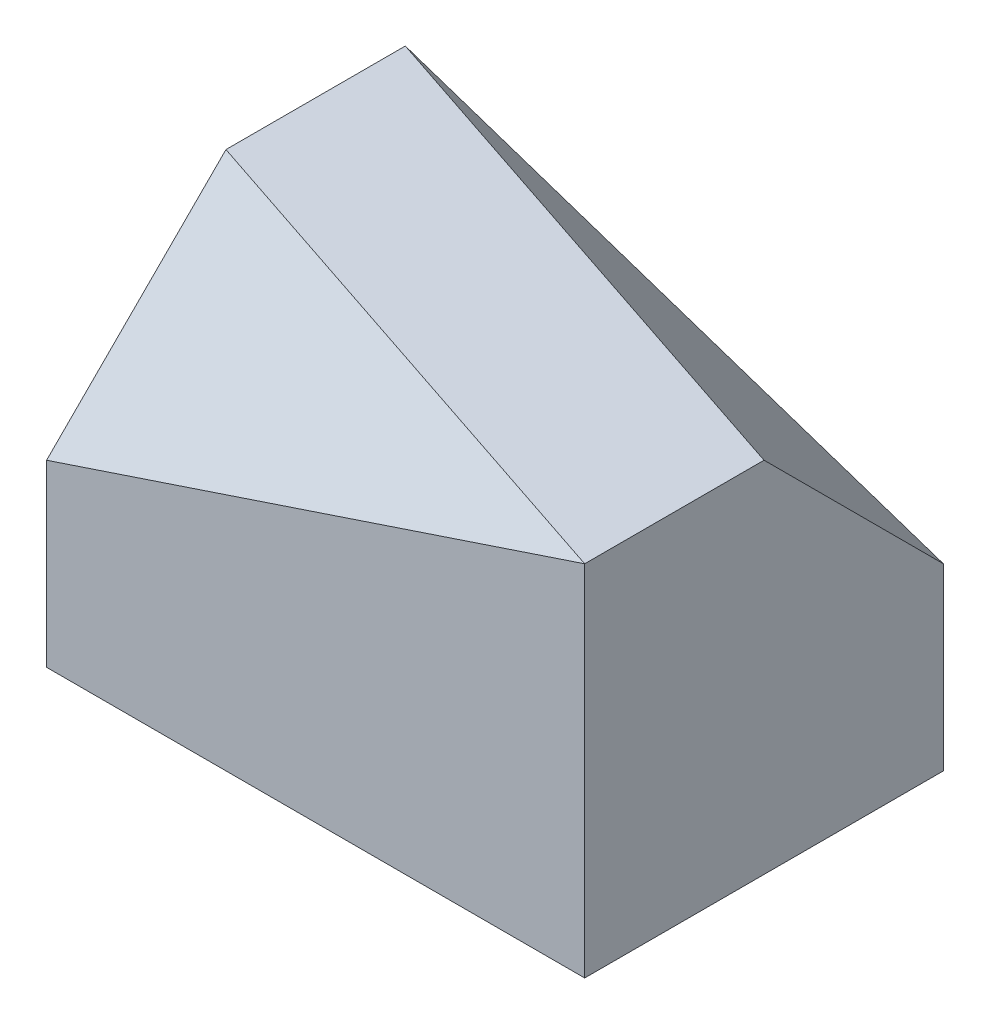
SolidWorks part; units mm, degrees
ref_plane "前基準面" through (0, 0, 0) normal (0, 0, 1) x (1, 0, 0)
ref_plane "上基準面" through (0, 0, 0) normal (0, 1, 0) x (1, 0, 0)
ref_plane "右基準面" through (0, 0, 0) normal (1, 0, 0) x (0, 0, -1)
sketch "草圖1" plane through (0, 0, 0) normal (0, 1, 0) x (1, 0, 0)
  line L1 (-15, -10) -> (15, -10)
  line L2 (-15, -10) -> (-15, 10)
  line L3 (-15, 10) -> (15, 10)
  line L4 (15, -10) -> (15, 10)
  line L5 (-15, -10) -> (15, 10) construction
  line L6 (-15, 10) -> (15, -10) construction
  point P0 (0, 0)
  dimension "D1" = 30
  dimension "D2" = 20
extrude "填料-伸長1" add sketch "草圖1" along normal blind 20
sketch "草圖2" plane through (15, 0, 0) normal (1, 0, 0) x (0, 0, -1)
  line L0 (10, 10) -> (0, 20)
  line L1 (10, 20) -> (10, 0) construction
  line L2 (-10, 20) -> (10, 20) construction
  dimension "D1" = 10
  dimension "D2" = 10
sketch "草圖4" plane through (0, 20, 0) normal (0, 1, 0) x (1, 0, 0)
  line L0 (-15, 10) -> (15, 0)
  line L1 (15, 10) -> (15, 0) construction
  dimension "D1" = 10
sketch "草圖5" plane through (0, 0, -10) normal (0, 0, -1) x (-1, 0, 0)
  line L0 (-15, 10) -> (15, 20)
  line L1 (-15, 20) -> (-15, 0) construction
  line L2 (15, 20) -> (-15, 20) construction
ref_plane "平面1" through (3.9474, 11.8421, -11.8421) normal (-0.2294, -0.6882, 0.6882) x (0.9733, -0.1622, 0.1622)
sketch "草圖6" plane through (3.9474, 11.8421, -11.8421) normal (-0.2294, -0.6882, 0.6882) x (0.9733, -0.1622, 0.1622)
  line L0 (0, 0) -> (-20.5388, 0)
  line L1 (-20.5388, 0) -> (-20.5388, 12.5352)
  line L2 (-20.5388, 12.5352) -> (11.7135, 14.6256)
  line L3 (11.7135, 14.6256) -> (12.2681, -0.2633)
  line L4 (12.2681, -0.2633) -> (0, 0)
extrude "除料-伸長1" cut sketch "草圖6" against normal blind 20
sketch "草圖8" plane through (-15, 0, 0) normal (-1, 0, 0) x (0, 0, 1)
  line L0 (10, 10) -> (0, 20)
  line L1 (10, 20) -> (10, 0) construction
  line L2 (-10, 20) -> (10, 20) construction
  dimension "D1" = 10
  dimension "D2" = 10
sketch "草圖9" plane through (0, 20, 0) normal (0, 1, 0) x (1, 0, 0)
  line L0 (-15, 0) -> (15, -10)
  line L1 (-15, 10) -> (-15, -10) construction
ref_plane "平面2" through (-3.9474, 11.8421, 11.8421) normal (-0.2294, 0.6882, 0.6882) x (0.9733, 0.1622, 0.1622)
sketch "草圖10" plane through (-3.9474, 11.8421, 11.8421) normal (-0.2294, 0.6882, 0.6882) x (0.9733, 0.1622, 0.1622)
  line L1 (-12.1828, -0.4751) -> (20.0695, -0.4751)
  line L2 (-12.1828, -0.4751) -> (-12.1828, 14.7041)
  line L3 (-12.1828, 14.7041) -> (20.0695, 14.7041)
  line L4 (20.0695, -0.4751) -> (20.0695, 14.7041)
extrude "除料-伸長2" cut sketch "草圖10" along normal blind 25
